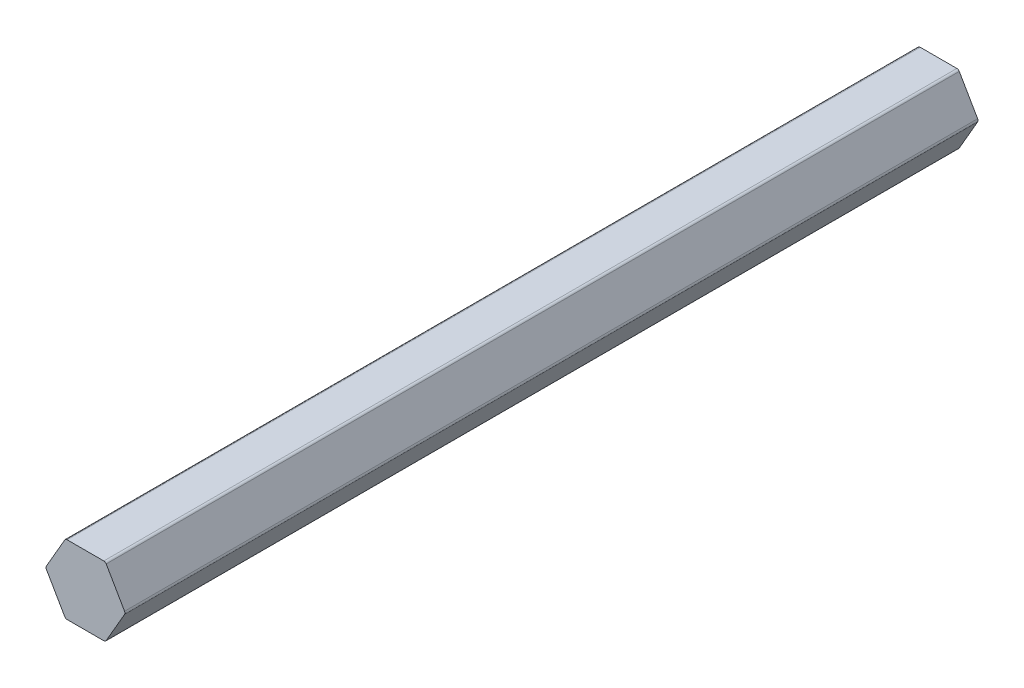
SolidWorks part; units mm, degrees
ref_plane "Front Plane" through (0, 0, 0) normal (0, 0, 1) x (1, 0, 0)
ref_plane "Top Plane" through (0, 0, 0) normal (0, 1, 0) x (1, 0, 0)
ref_plane "Right Plane" through (0, 0, 0) normal (1, 0, 0) x (0, 0, -1)
ref_plane "Plane1" through (0, 0, -228.6) normal (0, 0, -1) x (-1, 0, 0)
sketch "Sketch1" plane through (0, 0, -228.6) normal (0, 0, -1) x (-1, 0, 0)
  line L0 (3.8055, -6.0833) -> (7.171, -0.254)
  line L1 (7.171, 0.254) -> (3.8055, 6.0833)
  line L2 (3.3655, 6.3373) -> (-3.3655, 6.3373)
  line L3 (-3.8055, 6.0833) -> (-7.171, 0.254)
  line L4 (-7.171, -0.254) -> (-3.8055, -6.0833)
  line L5 (-3.3655, -6.3373) -> (3.3655, -6.3373)
  arc A0 (3.3655, -6.3373) -> (3.8055, -6.0833) centre (3.3655, -5.8293) ccw
  arc A1 (7.171, -0.254) -> (7.171, 0.254) centre (6.7311, 0) ccw
  arc A2 (3.8055, 6.0833) -> (3.3655, 6.3373) centre (3.3655, 5.8293) ccw
  arc A3 (-3.3655, 6.3373) -> (-3.8055, 6.0833) centre (-3.3655, 5.8293) ccw
  arc A4 (-7.171, 0.254) -> (-7.171, -0.254) centre (-6.7311, 0) ccw
  arc A5 (-3.8055, -6.0833) -> (-3.3655, -6.3373) centre (-3.3655, -5.8293) ccw
extrude "Boss-Extrude1" add sketch "Sketch1" against normal blind 156.464
